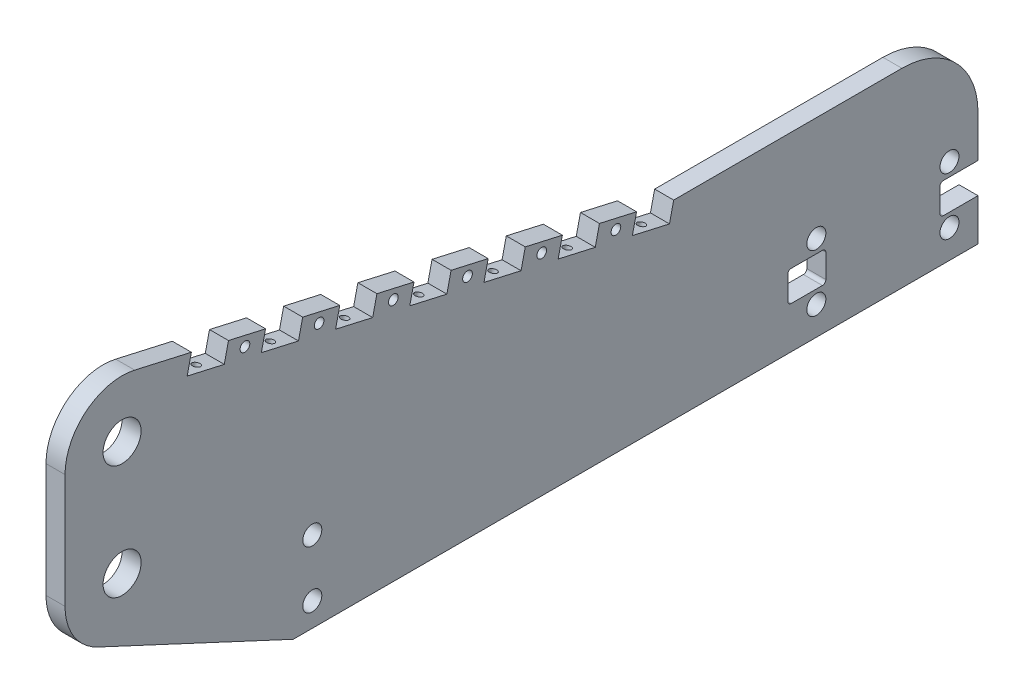
SolidWorks part; units mm, degrees
material "7075-T6 (SN)"
ref_plane "Front Plane" through (0, 0, 0) normal (0, 0, 1) x (1, 0, 0)
ref_plane "Top Plane" through (0, 0, 0) normal (0, 1, 0) x (1, 0, 0)
ref_plane "Right Plane" through (0, 0, 0) normal (1, 0, 0) x (0, 0, -1)
sketch "Sketch1" plane through (0, 0, 0) normal (1, 0, 0) x (0, 0, -1)
  line L0 (-38.1, 76.2) -> (-38.1, 0)
  line L1 (114.3, -95.25) -> (571.5, -95.25)
  line L2 (571.5, -95.25) -> (571.5, 31.75)
  line L3 (8.4258, 113.3566) -> (368.3, 31.75)
  line L4 (114.3, -95.25) -> (-16.0827, -34.5392)
  line L5 (368.3, 31.75) -> (571.5, 31.75)
  circle A0 centre (0, 0) radius 12.7
  circle A1 centre (0, 76.2) radius 12.7
  circle A2 centre (0, 0) radius 38.1
  circle A3 centre (0, 76.2) radius 38.1
  dimension "D1" = 25.4
  dimension "D2" = 25.4
  dimension "D3" = 76.2
  dimension "D6" = 127
  dimension "D7" = 457.2
  dimension "D8" = 95.25
  dimension "D9" = 571.5
  dimension "D10" = 203.2
  dimension "D4" = 25.4
  dimension "D5" = 25.4
extrude "Boss-Extrude1" add sketch "Sketch1" along normal blind 12.7 contours A3 A2 L1 L2 L5 | A3 A2 A1 | A2 A3 | A3 A2 A0 | A3 L0 A2
sketch "Sketch2" plane through (12.7, 0, 0) normal (1, 0, 0) x (0, 0, -1)
  line L0 (114.3, -95.25) -> (571.5, -95.25) construction
  line L1 (463.55, -38.1) -> (552.45, -38.1)
  line L2 (463.55, -38.1) -> (463.55, -76.2)
  line L3 (463.55, -76.2) -> (552.45, -76.2)
  line L4 (552.45, -38.1) -> (552.45, -76.2)
  line L5 (463.55, -38.1) -> (552.45, -76.2) construction
  line L6 (463.55, -76.2) -> (552.45, -38.1) construction
  line L7 (571.5, -95.25) -> (571.5, 31.75) construction
  circle A0 centre (552.45, -38.1) radius 6.35
  circle A1 centre (463.55, -38.1) radius 6.35
  circle A2 centre (463.55, -76.2) radius 6.35
  circle A3 centre (552.45, -76.2) radius 6.35
  point P0 (508, -57.15)
  dimension "D5" = 12.7
  dimension "D1" = 88.9
  dimension "D2" = 38.1
  dimension "D3" = 19.05
  dimension "D4" = 19.05
extrude "Cut-Extrude1" cut sketch "Sketch2" against normal through all contours A1 | A0 | A3 | A2
sketch "Sketch3" plane through (12.7, 0, 0) normal (1, 0, 0) x (0, 0, -1)
  line L0 (127, -95.25) -> (127, -79.375)
  line L1 (114.3, -95.25) -> (571.5, -95.25) construction
  line L2 (127, -79.375) -> (127, -41.275)
  circle A0 centre (127, -41.275) radius 6.35
  circle A1 centre (127, -79.375) radius 6.35
  dimension "D1" = 15.875
  dimension "D3" = 12.7
  dimension "D2" = 38.1
  dimension "D4" = 12.7
extrude "Cut-Extrude2" cut sketch "Sketch3" against normal through all contours A0 | A1
sketch "Sketch4" plane through (12.7, 0, 0) normal (1, 0, 0) x (0, 0, -1)
  line L0 (571.5, -95.25) -> (571.5, 31.75) construction
  line L1 (571.5, -46.99) -> (546.1, -46.99)
  line L2 (571.5, -46.99) -> (571.5, -67.31)
  line L3 (571.5, -67.31) -> (546.1, -67.31)
  line L4 (546.1, -46.99) -> (546.1, -67.31)
  line L5 (114.3, -95.25) -> (571.5, -95.25) construction
  line L6 (444.5, -46.99) -> (469.9, -46.99)
  line L7 (444.5, -46.99) -> (444.5, -67.31)
  line L8 (444.5, -67.31) -> (469.9, -67.31)
  line L9 (469.9, -46.99) -> (469.9, -67.31)
  dimension "D1" = 25.4
  dimension "D2" = 127
  dimension "D3" = 20.32
  dimension "D4" = 27.94
  dimension "D5" = 25.4
  dimension "D6" = 20.32
  dimension "D7" = 27.94
extrude "Cut-Extrude3" cut sketch "Sketch4" against normal through all
fillet "Fillet1" radius 2.286 6 edges at (6.35, -67.31, -546.1) (6.35, -46.99, -546.1) (6.35, -46.99, -469.9) (6.35, -67.31, -469.9) (6.35, -67.31, -444.5) (6.35, -46.99, -444.5)
sketch "Sketch5" plane through (12.7, 0, 0) normal (1, 0, 0) x (0, 0, -1)
  line L0 (368.3, 31.75) -> (343.5289, 37.3672)
  line L1 (368.3, 31.75) -> (365.4914, 19.3645)
  line L2 (343.5289, 37.3672) -> (340.7203, 24.9817)
  line L3 (365.4914, 19.3645) -> (340.7203, 24.9817)
  line L4 (8.4258, 113.3566) -> (368.3, 31.75) construction
  line L5 (293.9867, 48.6016) -> (291.1781, 36.2161)
  line L6 (318.7578, 42.9844) -> (293.9867, 48.6016)
  line L7 (318.7578, 42.9844) -> (315.9492, 30.5989)
  line L8 (315.9492, 30.5989) -> (291.1781, 36.2161)
  line L9 (244.4445, 59.836) -> (241.6359, 47.4505)
  line L10 (269.2156, 54.2188) -> (244.4445, 59.836)
  line L11 (269.2156, 54.2188) -> (266.407, 41.8333)
  line L12 (266.407, 41.8333) -> (241.6359, 47.4505)
  line L13 (194.9023, 71.0704) -> (192.0937, 58.6849)
  line L14 (219.6734, 65.4532) -> (194.9023, 71.0704)
  line L15 (219.6734, 65.4532) -> (216.8648, 53.0677)
  line L16 (216.8648, 53.0677) -> (192.0937, 58.6849)
  line L17 (145.3602, 82.3048) -> (142.5516, 69.9193)
  line L18 (170.1313, 76.6876) -> (145.3602, 82.3048)
  line L19 (170.1313, 76.6876) -> (167.3227, 64.3021)
  line L20 (167.3227, 64.3021) -> (142.5516, 69.9193)
  line L21 (95.818, 93.5392) -> (93.0094, 81.1537)
  line L22 (120.5891, 87.922) -> (95.818, 93.5392)
  line L23 (120.5891, 87.922) -> (117.7805, 75.5365)
  line L24 (117.7805, 75.5365) -> (93.0094, 81.1537)
  line L25 (46.2758, 104.7736) -> (43.4672, 92.3881)
  line L26 (71.0469, 99.1564) -> (46.2758, 104.7736)
  line L27 (71.0469, 99.1564) -> (68.2383, 86.7709)
  line L28 (68.2383, 86.7709) -> (43.4672, 92.3881)
  dimension "D1" = 12.7
  dimension "D2" = 25.4
  dimension "D3" = 7
extrude "Cut-Extrude4" cut sketch "Sketch5" against normal through all
sketch "Sketch6" plane through (12.7, 0, 0) normal (1, 0, 0) x (0, 0, -1)
  line L0 (343.5289, 37.3672) -> (315.9492, 30.5989) construction
  circle A0 centre (329.7391, 33.983) radius 3.2385
  circle A1 centre (280.1969, 45.2174) radius 3.2385
  circle A2 centre (230.6547, 56.4518) radius 3.2385
  circle A3 centre (181.1125, 67.6862) radius 3.2385
  circle A4 centre (131.5703, 78.9206) radius 3.2385
  circle A5 centre (82.0281, 90.155) radius 3.2385
  dimension "D1" = 6.477
  dimension "D2" = 6
extrude "Cut-Extrude5" cut sketch "Sketch6" against normal through all
sketch "Sketch7" plane through (0, 97.2444, -22.0516) normal (0, 0.9752, -0.2211) x (1, 0, 0)
  line L0 (0, 352.1593) -> (12.7, 326.7593) construction
  circle A0 centre (6.35, 339.4593) radius 2.5527
  circle A1 centre (6.35, 288.6593) radius 2.5527
  circle A2 centre (6.35, 237.8593) radius 2.5527
  circle A3 centre (6.35, 187.0593) radius 2.5527
  circle A4 centre (6.35, 136.2593) radius 2.5527
  circle A5 centre (6.35, 85.4593) radius 2.5527
  circle A6 centre (6.35, 34.6593) radius 2.5527
  dimension ".201" = 5.1054
  dimension "D2" = 7
extrude "Cut-Extrude6" cut sketch "Sketch7" against normal blind 25.4
sketch "Sketch8" plane through (0, 0, 0) normal (1, 0, 0) x (0, 0, -1)
  circle A0 centre (82.0281, 90.155) radius 5.08
  circle A1 centre (131.5703, 78.9206) radius 5.08
  circle A2 centre (181.1125, 67.6862) radius 5.08
  circle A3 centre (230.6547, 56.4518) radius 5.08
  circle A4 centre (280.1969, 45.2174) radius 5.08
  circle A5 centre (329.7391, 33.983) radius 5.08
  dimension "D1" = 10.16
  dimension "D2" = 6
extrude "Cut-Extrude7" cut sketch "Sketch8" along normal blind 6.35
fillet "Fillet2" radius 50.8 1 edges at (6.35, 31.75, -571.5)
sketch "Sketch10" plane through (0, 0, 0) normal (1, 0, 0) x (0, 0, -1)
  line L44 (364.8284, -6.5301) -> (34.7052, 68.3301)
  line L46 (550.2121, -19.05) -> (463.55, -19.05)
  line L47 (431.8, -49.276) -> (431.8, -65.024)
  line L48 (431.8, -51.7621) -> (431.8, -74.93)
  line L49 (368.3, 31.75) -> (520.7, 31.75) construction
  line L50 (448.1654, -26.8654) -> (433.2662, -47.2682)
  line L51 (25.4, 60.8988) -> (25.4, 0)
  line L81 (558.8, -34.29) -> (558.8, -19.05)
  line L82 (520.7, 19.05) -> (378.4425, 19.05)
  line L83 (378.4425, 19.05) -> (375.0683, 4.1703)
  line L84 (375.0683, 4.1703) -> (28.273, 82.8111)
  line L85 (28.273, 82.8111) -> (31.0816, 95.1967)
  line L86 (31.0816, 95.1967) -> (5.6172, 100.9711)
  line L87 (-25.4, 76.2) -> (-25.4, 0)
  line L88 (-10.7218, -23.0261) -> (117.1118, -82.55)
  line L89 (117.1118, -82.55) -> (558.8, -82.55)
  line L90 (558.8, -82.55) -> (558.8, -80.01)
  line L91 (558.8, -80.01) -> (548.386, -80.01)
  line L92 (533.4, -65.024) -> (533.4, -49.276)
  line L93 (548.386, -34.29) -> (558.8, -34.29)
  line L95 (520.7, 19.05) -> (384.528, 19.05)
  line L96 (377.0967, 13.1152) -> (373.9449, -0.7839)
  line L101 (14.5021, -34.7713) -> (99.8512, -74.5128)
  line L102 (153.297, -82.55) -> (424.18, -82.55)
  arc A0 (14.5021, -34.7713) -> (13.6297, -21.4334) centre (17.7186, -27.8634) cw
  arc A1 (25.4, 60.8988) -> (34.7052, 68.3301) centre (33.02, 60.8988) cw
  arc A2 (113.6678, -65.7679) -> (113.6678, -54.8821) centre (108.3349, -60.325) ccw
  arc A3 (140.3322, -65.7679) -> (140.3322, -54.8821) centre (145.6651, -60.325) cw
  arc A4 (145.7836, -76.2) -> (140.3322, -65.7679) centre (127, -79.375) ccw
  arc A5 (153.297, -82.55) -> (145.7836, -76.2) centre (153.297, -74.93) cw
  arc A6 (109.9055, -70.9678) -> (99.8512, -74.5128) centre (103.0677, -67.605) cw
  circle A89 centre (0, 0) radius 25.4
  arc A90 (13.6297, -21.4334) -> (25.4, 0) centre (0, 0) ccw
  arc A92 (558.8, -19.05) -> (520.7, 19.05) centre (520.7, -19.05) ccw
  arc A93 (5.6172, 100.9711) -> (-25.4, 76.2) centre (0, 76.2) ccw
  arc A94 (-25.4, 0) -> (-10.7218, -23.0261) centre (0, 0) ccw
  arc A95 (533.4, -65.024) -> (548.386, -80.01) centre (548.386, -65.024) ccw
  arc A96 (548.386, -34.29) -> (533.4, -49.276) centre (548.386, -49.276) ccw
  arc A97 (557.5902, -9.525) -> (520.7, 19.05) centre (520.7, -19.05) ccw
  arc A98 (557.5902, -9.525) -> (550.2121, -19.05) centre (550.2121, -11.43) cw
  arc A100 (364.8284, -6.5301) -> (373.9449, -0.7839) centre (366.5136, 0.9012) ccw
  arc A101 (384.528, 19.05) -> (377.0967, 13.1152) centre (384.528, 11.43) ccw
  circle A105 centre (127, -41.275) radius 19.05
  arc A106 (140.3322, -54.8821) -> (113.6678, -54.8821) centre (127, -41.275) ccw
  circle A108 centre (127, -79.375) radius 19.05
  arc A109 (113.6678, -65.7679) -> (109.9055, -70.9678) centre (127, -79.375) ccw
  arc A110 (433.2662, -47.2682) -> (431.8, -51.7621) centre (439.42, -51.7621) ccw
  circle A111 centre (463.55, -38.1) radius 19.05
  arc A112 (463.55, -19.05) -> (448.1654, -26.8654) centre (463.55, -38.1) ccw
  arc A113 (424.18, -82.55) -> (431.8, -74.93) centre (424.18, -74.93) ccw
  dimension "D2" = 7.62
  dimension "D9" = 7.62
  dimension "D4" = 7.62
  dimension "D10" = 7.62
  dimension "D11" = 7.62
  dimension "D12" = 7.62
  dimension "D1" = 12.7
  dimension "D3" = 12.7
  dimension "D5" = 12.7
  dimension "D6" = 12.7
  dimension "D7" = 12.7
  dimension "D8" = 12.7
extrude "Cut-Extrude9" cut sketch "Sketch10" along normal blind 6.35
sketch "Sketch11" plane through (6.35, 0, 0) normal (-1, 0, 0) x (0, 0, 1)
  line L0 (-448.4905, -20.8546) -> (-404.6568, 7.3605)
  line L1 (-438.0893, -29.2631) -> (-385.6044, 4.5207)
  line L2 (-376.828, 2.6182) -> (-328.3062, -72.7631)
  line L3 (-352.0735, -12.3751) -> (-311.382, -75.5915)
  line L4 (-301.3407, -76.4225) -> (-218.5362, 14.7984)
  line L5 (-280.1126, -71.932) -> (-188.9611, 28.4842)
  line L6 (-178.9199, 27.6531) -> (-144.2454, -26.2155)
  line L7 (-165.3114, 29.9759) -> (-133.5664, -19.3416)
  line L8 (-115.1639, -21.6766) -> (-29.7902, 57.2941)
  line L9 (-106.5401, -30.9996) -> (-36.0619, 34.1927)
  line L10 (-127, -41.275) -> (0, 76.2) construction
  line L11 (-153.297, -82.55) -> (-275.4108, -82.55)
  line L12 (-384.528, 19.05) -> (-408.0937, 19.05)
  line L13 (-333.6456, -82.55) -> (-275.4108, -82.55)
  line L14 (-463.55, -19.05) -> (-439.7806, -38.3475)
  line L15 (-224.6423, 25.2591) -> (-201.3516, 30.5406)
  line L16 (-196.3726, 31.6697) -> (-161.3763, 39.6056)
  line L17 (-143.9386, -32.5581) -> (-108.4211, -37.0646)
  line L18 (-25.4, 29.5311) -> (-25.4, 60.8988)
  line L33 (-25.4, 0) -> (-25.4, 60.8988)
  line L34 (-34.7052, 68.3301) -> (-47.746, 65.3729)
  line L35 (-47.746, 65.3729) -> (-52.725, 64.2438)
  line L36 (-52.725, 64.2438) -> (-97.2882, 54.1385)
  line L37 (-97.2882, 54.1385) -> (-102.2672, 53.0094)
  line L38 (-102.2672, 53.0094) -> (-146.8304, 42.9041)
  line L39 (-146.8304, 42.9041) -> (-151.8094, 41.775)
  line L40 (-151.8094, 41.775) -> (-196.3726, 31.6697)
  line L41 (-196.3726, 31.6697) -> (-201.3516, 30.5406)
  line L42 (-201.3516, 30.5406) -> (-245.9148, 20.4353)
  line L43 (-245.9148, 20.4353) -> (-250.8938, 19.3062)
  line L44 (-250.8938, 19.3062) -> (-295.457, 9.2009)
  line L45 (-295.457, 9.2009) -> (-300.436, 8.0718)
  line L46 (-300.436, 8.0718) -> (-344.9992, -2.0335)
  line L47 (-344.9992, -2.0335) -> (-349.9781, -3.1626)
  line L48 (-349.9781, -3.1626) -> (-364.8284, -6.5301)
  line L49 (-373.9449, -0.7839) -> (-377.0967, 13.1152)
  line L50 (-384.528, 19.05) -> (-520.7, 19.05)
  line L51 (-550.2121, -19.05) -> (-463.55, -19.05)
  line L52 (-448.1654, -26.8654) -> (-433.2662, -47.2682)
  line L53 (-431.8, -51.7621) -> (-431.8, -74.93)
  line L54 (-424.18, -82.55) -> (-153.297, -82.55)
  line L55 (-99.8512, -74.5128) -> (-14.5021, -34.7713)
  line L56 (-25.4, 0) -> (-25.4, 29.5311)
  line L57 (-35.5064, 68.1484) -> (-47.746, 65.3729)
  line L58 (-47.746, 65.3729) -> (-52.725, 64.2438)
  line L59 (-52.725, 64.2438) -> (-97.2882, 54.1385)
  line L60 (-97.2882, 54.1385) -> (-102.2672, 53.0094)
  line L61 (-102.2672, 53.0094) -> (-146.8304, 42.9041)
  line L62 (-146.8304, 42.9041) -> (-151.8094, 41.775)
  line L63 (-151.8094, 41.775) -> (-161.3763, 39.6056)
  line L64 (-196.3726, 31.6697) -> (-201.3516, 30.5406)
  line L65 (-224.6423, 25.2591) -> (-245.9148, 20.4353)
  line L66 (-245.9148, 20.4353) -> (-250.8938, 19.3062)
  line L67 (-250.8938, 19.3062) -> (-295.457, 9.2009)
  line L68 (-295.457, 9.2009) -> (-300.436, 8.0718)
  line L69 (-300.436, 8.0718) -> (-348.1383, -2.7454)
  line L70 (-344.9992, -2.0335) -> (-349.9781, -3.1626)
  line L71 (-349.9781, -3.1626) -> (-364.8284, -6.5301)
  line L72 (-373.9449, -0.7839) -> (-377.0967, 13.1152)
  line L73 (-408.0937, 19.05) -> (-520.7, 19.05)
  line L74 (-550.2121, -19.05) -> (-463.55, -19.05)
  line L75 (-439.7806, -38.3475) -> (-433.2662, -47.2682)
  line L76 (-431.8, -51.7621) -> (-431.8, -74.93)
  line L77 (-424.18, -82.55) -> (-333.6456, -82.55)
  line L78 (-99.8512, -74.5128) -> (-14.5021, -34.7713)
  arc A0 (-35.5064, 68.1484) -> (-29.7902, 57.2941) centre (-34.1021, 61.9556) cw
  circle A1 centre (-127, -41.275) radius 6.35 construction
  circle A2 centre (-463.55, -38.1) radius 6.35 construction
  arc A3 (-25.4, 29.5311) -> (-36.0619, 34.1927) centre (-31.75, 29.5311) ccw
  arc A4 (-161.3763, 39.6056) -> (-165.3114, 29.9759) centre (-159.972, 33.4128) ccw
  arc A5 (-143.9386, -32.5581) -> (-144.2454, -26.2155) centre (-149.5849, -29.6524) ccw
  arc A6 (-178.9199, 27.6531) -> (-188.9611, 28.4842) centre (-184.2593, 24.2162) ccw
  arc A7 (-224.6423, 25.2591) -> (-218.5362, 14.7984) centre (-223.238, 19.0664) cw
  arc A8 (-348.1383, -2.7454) -> (-352.0735, -12.3751) centre (-346.734, -8.9381) ccw
  arc A9 (-311.382, -75.5915) -> (-301.3407, -76.4225) centre (-306.0425, -72.1545) ccw
  arc A10 (-333.6456, -82.55) -> (-328.3062, -72.7631) centre (-333.6456, -76.2) ccw
  arc A11 (-439.7806, -38.3475) -> (-438.0893, -29.2631) centre (-434.6524, -34.6026) cw
  arc A12 (-376.828, 2.6182) -> (-385.6044, 4.5207) centre (-382.1675, -0.8188) ccw
  arc A13 (-404.6568, 7.3605) -> (-408.0937, 19.05) centre (-408.0937, 12.7) ccw
  arc A14 (-448.4905, -20.8546) -> (-454.8331, -21.1614) centre (-451.9274, -15.5151) cw
  arc A15 (-275.4108, -82.55) -> (-280.1126, -71.932) centre (-275.4108, -76.2) cw
  arc A16 (-143.9386, -32.5581) -> (-140.3322, -54.8821) centre (-127, -41.275) ccw
  arc A17 (-121.3569, -23.08) -> (-127.9202, -22.2472) centre (-127, -41.275) ccw
  arc A18 (-14.5021, -34.7713) -> (-13.6297, -21.4334) centre (-17.7186, -27.8634) ccw
  arc A19 (-25.4, 0) -> (-13.6297, -21.4334) centre (0, 0) ccw
  arc A20 (-25.4, 60.8988) -> (-34.7052, 68.3301) centre (-33.02, 60.8988) ccw
  arc A21 (-373.9449, -0.7839) -> (-364.8284, -6.5301) centre (-366.5136, 0.9012) ccw
  arc A22 (-377.0967, 13.1152) -> (-384.528, 19.05) centre (-384.528, 11.43) ccw
  arc A23 (-520.7, 19.05) -> (-557.5902, -9.525) centre (-520.7, -19.05) ccw
  arc A24 (-557.5902, -9.525) -> (-550.2121, -19.05) centre (-550.2121, -11.43) ccw
  arc A25 (-448.1654, -26.8654) -> (-463.55, -19.05) centre (-463.55, -38.1) ccw
  arc A26 (-431.8, -51.7621) -> (-433.2662, -47.2682) centre (-439.42, -51.7621) ccw
  arc A27 (-431.8, -74.93) -> (-424.18, -82.55) centre (-424.18, -74.93) ccw
  arc A28 (-153.297, -82.55) -> (-145.7836, -76.2) centre (-153.297, -74.93) ccw
  arc A29 (-140.3322, -65.7679) -> (-145.7836, -76.2) centre (-127, -79.375) ccw
  arc A30 (-140.3322, -65.7679) -> (-140.3322, -54.8821) centre (-145.6651, -60.325) ccw
  arc A31 (-113.6678, -54.8821) -> (-140.3322, -54.8821) centre (-127, -41.275) ccw
  arc A32 (-113.6678, -54.8821) -> (-113.6678, -65.7679) centre (-108.3349, -60.325) ccw
  arc A33 (-109.9055, -70.9678) -> (-113.6678, -65.7679) centre (-127, -79.375) ccw
  arc A34 (-109.9055, -70.9678) -> (-99.8512, -74.5128) centre (-103.0677, -67.605) ccw
  arc A35 (-14.5021, -34.7713) -> (-13.6297, -21.4334) centre (-17.7186, -27.8634) ccw
  arc A36 (-25.4, 0) -> (-13.6297, -21.4334) centre (0, 0) ccw
  arc A37 (-25.4, 60.8988) -> (-34.7052, 68.3301) centre (-33.02, 60.8988) ccw
  arc A38 (-373.9449, -0.7839) -> (-364.8284, -6.5301) centre (-366.5136, 0.9012) ccw
  arc A39 (-377.0967, 13.1152) -> (-384.528, 19.05) centre (-384.528, 11.43) ccw
  arc A40 (-520.7, 19.05) -> (-557.5902, -9.525) centre (-520.7, -19.05) ccw
  arc A41 (-557.5902, -9.525) -> (-550.2121, -19.05) centre (-550.2121, -11.43) ccw
  arc A42 (-454.8331, -21.1614) -> (-463.55, -19.05) centre (-463.55, -38.1) ccw
  arc A43 (-431.8, -51.7621) -> (-433.2662, -47.2682) centre (-439.42, -51.7621) ccw
  arc A44 (-431.8, -74.93) -> (-424.18, -82.55) centre (-424.18, -74.93) ccw
  arc A45 (-153.297, -82.55) -> (-145.7836, -76.2) centre (-153.297, -74.93) ccw
  arc A46 (-140.3322, -65.7679) -> (-145.7836, -76.2) centre (-127, -79.375) ccw
  arc A47 (-140.3322, -65.7679) -> (-140.3322, -54.8821) centre (-145.6651, -60.325) ccw
  arc A48 (-113.6678, -54.8821) -> (-108.4211, -37.0646) centre (-127, -41.275) ccw
  arc A49 (-113.6678, -54.8821) -> (-113.6678, -65.7679) centre (-108.3349, -60.325) ccw
  arc A50 (-109.9055, -70.9678) -> (-113.6678, -65.7679) centre (-127, -79.375) ccw
  arc A51 (-109.9055, -70.9678) -> (-99.8512, -74.5128) centre (-103.0677, -67.605) ccw
  arc A52 (-115.1639, -21.6766) -> (-121.3569, -23.08) centre (-119.4758, -17.015) cw
  arc A53 (-133.5664, -19.3416) -> (-127.9202, -22.2472) centre (-128.227, -15.9047) ccw
  arc A54 (-108.4211, -37.0646) -> (-106.5401, -30.9996) centre (-102.2281, -35.6611) cw
  point P67 (-183.399, 34.6117)
  point P98 (-306.9029, -82.55)
  line M43 (-25.4, 0) -> (-25.4, 60.8988)
  arc M44 (-25.4, 60.8988) -> (-34.7052, 68.3301) centre (-33.02, 60.8988) ccw
  line M45 (-34.7052, 68.3301) -> (-47.746, 65.3729)
  line M51 (-151.8094, 41.775) -> (-196.3726, 31.6697)
  line M52 (-196.3726, 31.6697) -> (-201.3516, 30.5406)
  line M53 (-201.3516, 30.5406) -> (-245.9148, 20.4353)
  line M58 (-344.9992, -2.0335) -> (-349.9781, -3.1626)
  line M59 (-349.9781, -3.1626) -> (-364.8284, -6.5301)
  arc M60 (-364.8284, -6.5301) -> (-373.9449, -0.7839) centre (-366.5136, 0.9012) cw
  line M61 (-373.9449, -0.7839) -> (-377.0967, 13.1152)
  arc M62 (-377.0967, 13.1152) -> (-384.528, 19.05) centre (-384.528, 11.43) ccw
  line M63 (-384.528, 19.05) -> (-520.7, 19.05)
  arc M67 (-463.55, -19.05) -> (-448.1654, -26.8654) centre (-463.55, -38.1) cw
  line M68 (-448.1654, -26.8654) -> (-433.2662, -47.2682)
  line M72 (-424.18, -82.55) -> (-153.297, -82.55)
  arc M76 (-140.3322, -54.8821) -> (-113.6678, -54.8821) centre (-127, -41.275) cw
  dimension "D10" = 6.35
  dimension "D11" = 6.35
  dimension "D12" = 6.35
  dimension "D13" = 6.35
  dimension "D2" = 12.7
  dimension "D3" = 12.7
  dimension "D4" = 12.7
  dimension "D5" = 12.7
  dimension "D6" = 12.7
  dimension "D7" = 75
  dimension "D8" = 75
  dimension "D9" = 80
  dimension "D1" = 0
extrude "Boss-Extrude2" add sketch "Sketch11" along normal blind 3.81 contours A53 L7 A4 A7 L4 A9 L3 A8 A13 L0 A14 A11 L1 A12 L2 A10 A15 L5 A6 L6 A5 M51 M52 M53 M58 M59 M60 M61 M62 M63 M67 M68 M72 M76 | L10 A54 L9 A3 M76 M43 | L10 L18 A0 L8 A52 M76 M44 M45
